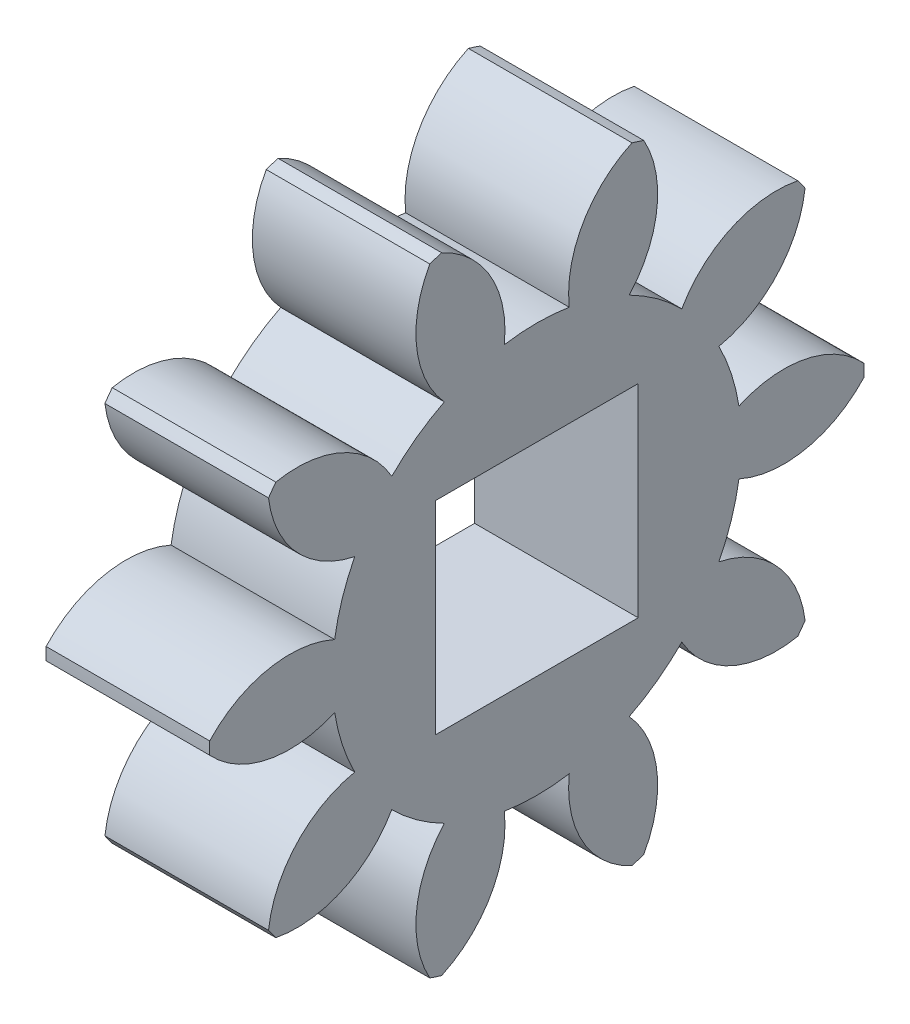
SolidWorks part; units mm, degrees
ref_plane "Plane1" through (0, 0, 0) normal (0, 0, 1) x (1, 0, 0)
ref_plane "Plane2" through (0, 0, 0) normal (0, 1, 0) x (1, 0, 0)
ref_plane "Plane3" through (0, 0, 0) normal (1, 0, 0) x (0, 0, -1)
sketch "HoldingSke" plane through (0, 0, 0) normal (0, 1, 0) x (1, 0, 0)
  line L0 (0, 0) -> (600.3388, -105.8559)
  line L1 (-15, 0) -> (100, 0) construction
  line L2 (0, 0) -> (-2.1039, 2.3779)
  line L3 (0, 0) -> (-11.863, 4.5341)
  line L4 (0, 0) -> (8.5048, 1.4996)
  line L5 (0, 0) -> (-47.5972, -17.7524)
  line L6 (0, 0) -> (-2.632, -1.7758)
  line L7 (-2.1039, 2.3779) -> (8.8308, 51.9871)
  line L8 (-76.2, 54.61) -> (-74.168, 54.61)
  line L9 (-71.009, 38.7566) -> (-53.1078, 45.2721)
  line L10 (-76.2, 71.12) -> (104.1128, 71.12)
  line L11 (0, 0) -> (-3.175, 0)
  line L12 (-76.2, 101.6) -> (-76.1573, 101.6)
  line L13 (24.9733, 27.94) -> (52.9518, 28.4284)
  line L14 (24.9733, 27.94) -> (25.0241, 27.9398)
  line L15 (24.9733, 27.94) -> (100.4021, 29.52)
  circle A0 centre (0, 0) radius 0.9995
  circle A1 centre (0, 0) radius 3.9709
  circle A2 centre (0, 0) radius 38.1
  circle A3 centre (0, 0) radius 0.9995
  dimension "MHD" = 7.9417
  dimension "Hub_dia" = 76.2
  dimension "Bore" = 1.999
  dimension "MBD" = 1.999
  dimension "Num_teeth" = 10
  dimension "Pitch" = 609.6
  dimension "Overall_len" = 50.8
  dimension "Show_teeth" = 10
  dimension "Thickness" = 3.175
  dimension "OAL" = 50.8001
  dimension "T_dim" = 2.032
  dimension "Ap" = 20
  dimension "H" = 19.05
  dimension "Pitch_radius" = 180.3128
  dimension "Width" = 3.175
  dimension "Backlash" = 0.0427
  dimension "Addendum_fac" = 1
  dimension "Dedendum_fac" = 1.2
  dimension "Clearance_fac" = 0.2
  dimension "Dedendum_add" = 0.0508
sketch "BasProSke" plane through (0, 0, 0) normal (0, 1, 0) x (1, 0, 0)
  line L0 (-10, 0) -> (60, 0) construction
  line L1 (0, 0) -> (0, 6.35)
  line L2 (0, 0) -> (3.175, 0)
  line L3 (3.175, 0) -> (3.175, 6.35)
  line L4 (3.175, 6.35) -> (0, 6.35)
  dimension "Thickness" = 3.175
  dimension "Diameter" = 12.7
revolve "Base-Revolve" add sketch "BasProSke" angle 360 about L0
sketch "TooCutSke" plane through (0, 0, 0) normal (1, 0, 0) x (0, 0, -1)
  line L1 (0, 0) -> (0, 107) construction
  line L2 (0, 0) -> (-0.9023, 5.2142) construction
  line L3 (0, 0) -> (-3.2371, 9.9629) construction
  line L4 (-0.9023, 5.2142) -> (-1.6186, 4.9814) construction
  arc A0 (0.6302, 3.9205) -> (-0.6302, 3.9205) centre (0, 0) ccw
  arc A1 (1.8823, 6.0912) -> (-1.8823, 6.0912) centre (0, 0) ccw
  circle A2 centre (0, 0) radius 5.2917 construction
  circle A3 centre (0, 0) radius 4.9725 construction
  arc A4 (-0.6302, 3.9205) -> (-1.8823, 6.0912) centre (-2.734, 4.1535) ccw
  arc A5 (1.8823, 6.0912) -> (0.6302, 3.9205) centre (2.734, 4.1535) ccw
  dimension "Root_dia" = 7.9417
  dimension "Overcut_dia" = 12.7508
  dimension "Pitch_dia" = 10.5833
  dimension "Base_dia" = 9.9451
  dimension "Flank_rad" = 2.1167
  dimension "Half_ang" = 18
  dimension "Half_CT" = 0.7531
extrude "ToothCut" cut sketch "TooCutSke" along normal through all
fillet "Breaks" [suppressed] radius 0.0212
fillet "RootFillets" [suppressed] radius 0.2625
pattern_circular "TeethCuts" count 10 every 36 about axis through (-10, 0, 0) along (1, 0, 0) of "ToothCut", "RootFillets", "Breaks"
sketch "HubNeaOneSke" plane through (0, 0, 0) normal (-1, 0, 0) x (0, 0, 1)
  circle A0 centre (0, 0) radius 3.9709
  dimension "Diameter" = 7.9417
extrude "HubNearOne" [suppressed] add sketch "HubNeaOneSke" along normal blind 47.6251
sketch "HubNeaBotSke" plane through (0, 0, 0) normal (-1, 0, 0) x (0, 0, 1)
  circle A0 centre (0, 0) radius 3.9709
  dimension "Diameter" = 7.9417
extrude "HubNearBoth" [suppressed] add sketch "HubNeaBotSke" along normal blind 23.8125
ref_plane "FarPln" through (3.175, 0, 0) normal (1, 0, 0) x (0, 0, -1)
sketch "HubFarSke" plane through (3.175, 0, 0) normal (1, 0, 0) x (0, 0, -1)
  circle A0 centre (0, 0) radius 3.9709
  dimension "Diameter" = 7.9417
extrude "HubFar" [suppressed] add sketch "HubFarSke" along normal blind 23.8125
sketch "BorSke" plane through (0, 0, 0) normal (1, 0, 0) x (0, 0, -1)
  circle A0 centre (0, 0) radius 0.9995
  dimension "Diameter" = 1.999
extrude "Bore" cut sketch "BorSke" along normal mid plane 101.6001
sketch "KeySke" plane through (0, 0, 0) normal (1, 0, 0) x (0, 0, -1)
  line L0 (-0.127, 0) -> (-0.127, 1.0325)
  line L1 (-0.127, 1.0325) -> (0.127, 1.0325)
  line L2 (0.127, 1.0325) -> (0.127, 0)
  line L3 (0, 0) -> (0, 34) construction
  line L4 (-0.127, 0) -> (0.127, 0)
  dimension "Offset" = 1.0325
  dimension "Width" = 0.254
extrude "Keyway" [suppressed] cut sketch "KeySke" along normal mid plane 101.6001
pattern_circular "Keyway2" [suppressed] count 2 every 90 about axis through (-10, 0, 0) along (1, 0, 0)
sketch "Sketch1" plane through (3.175, 0, 0) normal (1, 0, 0) x (0, 0, -1)
  line L1 (-1.9685, 1.9685) -> (1.9685, 1.9685)
  line L2 (-1.9685, 1.9685) -> (-1.9685, -1.9685)
  line L3 (-1.9685, -1.9685) -> (1.9685, -1.9685)
  line L4 (1.9685, 1.9685) -> (1.9685, -1.9685)
  line L5 (-1.9685, 1.9685) -> (1.9685, -1.9685) construction
  line L6 (-1.9685, -1.9685) -> (1.9685, 1.9685) construction
  point P0 (0, 0)
  dimension "D1" = 3.937
extrude "Cut-Extrude1" cut sketch "Sketch1" against normal through all both and the other way through all
equation "' \"Pitch@HoldingSke\" = 4"
equation "' \"Num_teeth@HoldingSke\" = 12"
equation "' \"Ap@HoldingSke\" =  20"
equation "' \"Ap@HoldingSke\" = 20"
equation "' \"Width@HoldingSke\" = 0.5"
equation "' \"Hub_dia@HoldingSke\"= 1"
equation "' \"Hub_dia@HoldingSke\" = 1"
equation "' \"Overall_len@HoldingSke\" = 1.0"
equation "' \"Bore@HoldingSke\" = 0.75"
equation "' \"T_dim@HoldingSke\" = 0.85"
equation "' \"Width@KeySke\" = 0.25"
equation "' \"Show_teeth@HoldingSke\" = 13"
equation "' \"Backlash@HoldingSke\" = 0.009"
equation "' \"Addendum_fac@HoldingSke\" = 1.0"
equation "' \"Dedendum_fac@HoldingSke\" = 1.25"
equation "' \"Dedendum_add@HoldingSke\" = 0.00005"
equation "' \"Clearance_fac@HoldingSke\" = 0.25"
equation "' \"Pitch@HoldingSke\" = 0.5"
equation "' \"Num_teeth@HoldingSke\" = 23"
equation "' \"Show_teeth@HoldingSke\" = 23"
equation "' \"Backlash@HoldingSke\" = 0.0375"
equation "\"Overcut_dia@TooCutSke\" = (\"Num_teeth@HoldingSke\" + 2 * \"Addendum_fac@HoldingSke\") / \"Pitch@HoldingSke\" + 0.002"
equation "\"Pitch_dia@TooCutSke\" = \"Num_teeth@HoldingSke\" / \"Pitch@HoldingSke\""
equation "\"Base_dia@TooCutSke\" = \"Num_teeth@HoldingSke\" / \"Pitch@HoldingSke\" * cos((\"Ap@HoldingSke\"  * 3.14159265 / 180))"
equation "\"Root_dia@TooCutSke\" = (\"Num_teeth@HoldingSke\" + 2) / \"Pitch@HoldingSke\" - 2 * (\"Addendum_fac@HoldingSke\" + \"Dedendum_fac@HoldingSke\") / \"Pitch@HoldingSke\" - \"Dedendum_add@HoldingSke\" * 2"
equation "\"Half_ang@TooCutSke\" = 180 / \"Num_teeth@HoldingSke\""
equation "\"Half_CT@TooCutSke\" = \"Num_teeth@HoldingSke\" / \"Pitch@HoldingSke\" * sin((3.14159265 / 2 / \"Num_teeth@HoldingSke\")) / 2 - 7 * \"Backlash@HoldingSke\" / 4"
equation "\"Flank_rad@TooCutSke\" = \"Num_teeth@HoldingSke\" / \"Pitch@HoldingSke\" / 5"
equation "\"Radius@RootFillets\" = \"Clearance_fac@HoldingSke\" / \"Pitch@HoldingSke\" + \"Dedendum_add@HoldingSke\""
equation "\"Break_rad@Breaks\" = 0.02 / \"Pitch@HoldingSke\""
equation "\"Thickness@HoldingSke\" = \"Width@HoldingSke\""
equation "\"OAL@HoldingSke\" = \"Thickness@HoldingSke\""
equation "\"MHD@HoldingSke\" = (\"Num_teeth@HoldingSke\" + 2) / \"Pitch@HoldingSke\" - 2 * (\"Addendum_fac@HoldingSke\" + \"Dedendum_fac@HoldingSke\")  / \"Pitch@HoldingSke\" - \"Dedendum_add@HoldingSke\" * 2"
equation "\"MBD@HoldingSke\" = (\"Num_teeth@HoldingSke\" + 2) / \"Pitch@HoldingSke\" - 2 * (\"Addendum_fac@HoldingSke\" + \"Dedendum_fac@HoldingSke\")  / \"Pitch@HoldingSke\" - \"Dedendum_add@HoldingSke\" * 2 - 0.002"
equation "\"MHD@HoldingSke\" = ((sgn( \"MHD@HoldingSke\" - \"Hub_dia@HoldingSke\" )-1)*( \"MHD@HoldingSke\" - \"Hub_dia@HoldingSke\" ))/-2+ \"Hub_dia@HoldingSke\""
equation "\"MBD@HoldingSke\" = ((sgn( \"MBD@HoldingSke\" - \"Bore@HoldingSke\" )-1)*( \"MBD@HoldingSke\" - \"Bore@HoldingSke\" ))/-2+ \"Bore@HoldingSke\""
equation "\"OAL@HoldingSke\" = ((sgn( \"OAL@HoldingSke\" - \"Overall_len@HoldingSke\" )+1)*( \"OAL@HoldingSke\" - \"Overall_len@HoldingSke\" ))/2 + \"Overall_len@HoldingSke\" + 0.000002"
equation "\"Num_teeth@TeethCuts\" = int( \"Show_teeth@HoldingSke\" ) + 1"
equation "\"Num_teeth@TeethCuts\" = ((sgn( \"Num_teeth@TeethCuts\" - \"Num_teeth@HoldingSke\" )-1)*( \"Num_teeth@TeethCuts\" - \"Num_teeth@HoldingSke\" ))/-2+ \"Num_teeth@HoldingSke\""
equation "\"Num_teeth@TeethCuts\" = ((sgn( \"Num_teeth@TeethCuts\" - 2.0)+1)*( \"Num_teeth@TeethCuts\" - 2.0))/2 +2.0"
equation "\"Angle@TeethCuts\" = 360.0 / \"Num_teeth@HoldingSke\""
equation "\"Diameter@BasProSke\" = (\"Num_teeth@HoldingSke\" + 2 * \"Addendum_fac@HoldingSke\") / \"Pitch@HoldingSke\""
equation "\"Thickness@BasProSke\"  = \"Thickness@HoldingSke\""
equation "' \"Fillet_rad@BasProSke\" =  \"Thickness@HoldingSke\" * 0.05"
equation "' \"Fillet_rad@BasProSke\" = \"Thickness@HoldingSke\" * 0.05"
equation "\"MHD@HoldingSke\" = ((sgn( \"MHD@HoldingSke\" - \"Root_dia@TooCutSke\" )-1)*( \"MHD@HoldingSke\" - \"Root_dia@TooCutSke\" ))/-2+ \"Root_dia@TooCutSke\""
equation "\"Diameter@HubNeaOneSke\" = \"MHD@HoldingSke\""
equation "\"Length@HubNearOne\" = \"OAL@HoldingSke\" - \"Thickness@BasProSke\""
equation "\"Diameter@HubNeaBotSke\" = \"MHD@HoldingSke\""
equation "\"Length@HubNearBoth\" = ( \"OAL@HoldingSke\" - \"Thickness@BasProSke\" ) / 2.0"
equation "\"Thickness@FarPln\" = \"Thickness@BasProSke\""
equation "\"Diameter@HubFarSke\" = \"MHD@HoldingSke\""
equation "\"Length@HubFar\" = ( \"OAL@HoldingSke\" - \"Thickness@BasProSke\" ) / 2.0"
equation "\"Diameter@BorSke\" = \"MBD@HoldingSke\""
equation "\"D1@Bore\" = \"OAL@HoldingSke\" * 2.0"
equation "\"D1@Keyway\" = \"OAL@HoldingSke\" * 2.0"
equation "\"Offset@KeySke\" = \"T_dim@HoldingSke\" - \"MBD@HoldingSke\" / 2.0"
